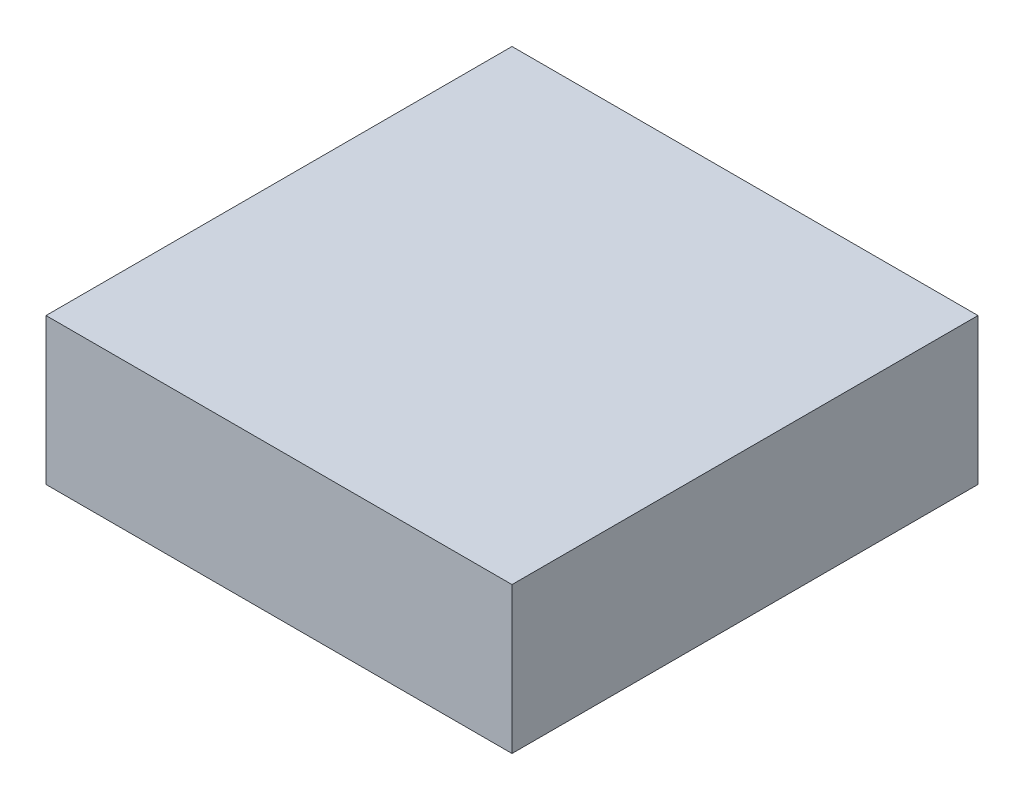
SolidWorks part; units mm, degrees
ref_plane "Front Plane" through (0, 0, 0) normal (0, 0, 1) x (1, 0, 0)
ref_plane "Top Plane" through (0, 0, 0) normal (0, 1, 0) x (1, 0, 0)
ref_plane "Right Plane" through (0, 0, 0) normal (1, 0, 0) x (0, 0, -1)
sketch "Sketch1" plane through (0, 0, 0) normal (0, 1, 0) x (1, 0, 0)
  line L1 (0, 0) -> (5, 0)
  line L2 (0, 0) -> (0, 5)
  line L3 (0, 5) -> (5, 5)
  line L4 (5, 0) -> (5, 5)
  dimension "D1" = 5
  dimension "D2" = 5
extrude "Boss-Extrude1" add sketch "Sketch1" along normal blind 1.57
